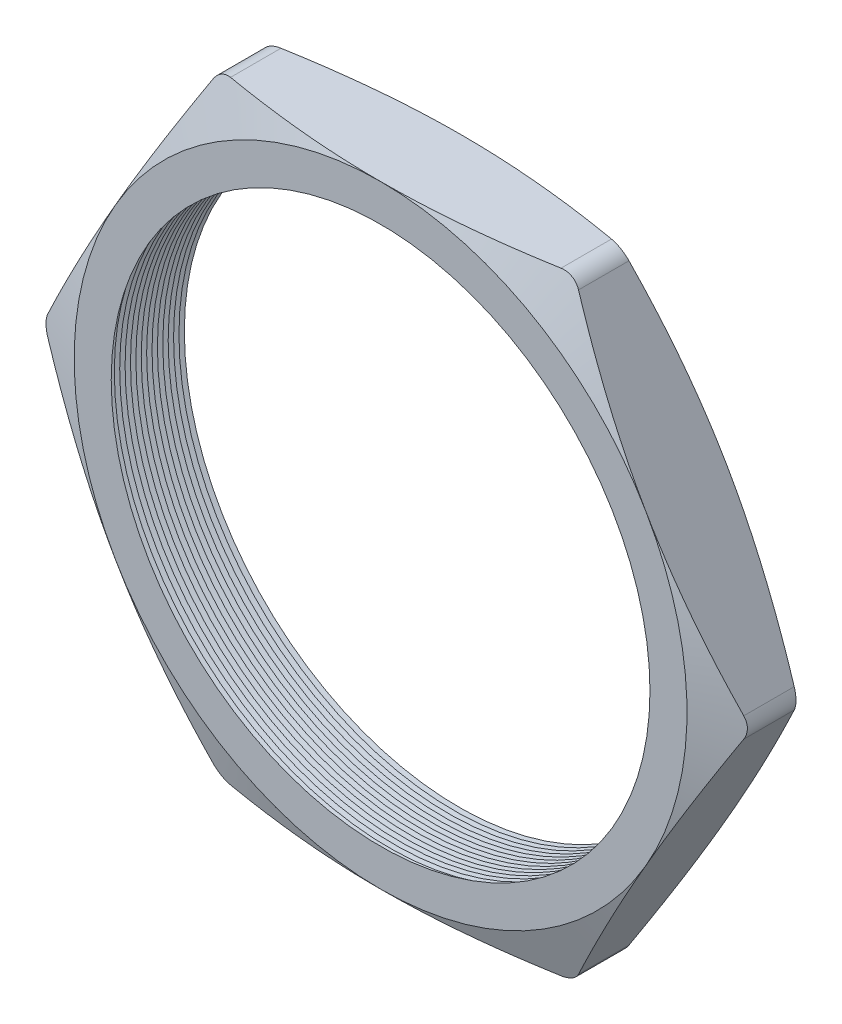
SolidWorks part; units mm, degrees
ref_plane "Front Plane" through (0, 0, 0) normal (0, 0, 1) x (1, 0, 0)
ref_plane "Top Plane" through (0, 0, 0) normal (0, 1, 0) x (1, 0, 0)
ref_plane "Right Plane" through (0, 0, 0) normal (1, 0, 0) x (0, 0, -1)
sketch "Sketch1" plane through (0, 0, 0) normal (0, 0, 1) x (1, 0, 0)
  line L1 (-13.3449, 0) -> (-6.6724, -11.557)
  line L2 (-6.6724, -11.557) -> (6.6724, -11.557)
  line L3 (6.6724, -11.557) -> (13.3449, 0)
  line L4 (13.3449, 0) -> (6.6724, 11.557)
  line L5 (6.6724, 11.557) -> (-6.6724, 11.557)
  line L6 (-6.6724, 11.557) -> (-13.3449, 0)
  circle A0 centre (0, 0) radius 11.557 construction
  circle A1 centre (0, 0) radius 10.16
  dimension "TS" = 20.32
  dimension "H" = 23.114
extrude "Extrude1" add sketch "Sketch1" along normal blind 3.048
fillet "Fillet1" radius 0.762 6 edges at (-6.6724, 11.557, 1.524) (-13.3449, 0, 1.524) (-6.6724, -11.557, 1.524) (6.6724, -11.557, 1.524) (13.3449, 0, 1.524) (6.6724, 11.557, 1.524)
sketch "Sketch2" plane through (0, 0, 3.048) normal (0, 0, 1) x (1, 0, 0)
  line L0 (6.2325, 11.557) -> (-6.2325, 11.557) construction
  circle A0 centre (0, 0) radius 11.557
extrude "Cut-Extrude1" cut sketch "Sketch2" against normal through all draft 70 flip side to cut
sketch "Sketch3" plane through (0, 0, 0) normal (0, 0, -1) x (-1, 0, 0)
  circle A0 centre (0, 0) radius 11.557
extrude "Cut-Extrude2" cut sketch "Sketch3" against normal through all draft 70 flip side to cut
sketch "Sketch4" plane through (0, 0, 0) normal (0, 1, 0) x (1, 0, 0)
  line L0 (-10.16, -3.048) -> (-10.16, -2.6081)
  line L2 (-10.16, -2.6081) -> (-10.541, -2.828)
  line L3 (-10.541, -2.828) -> (-10.16, -3.048)
  line L5 (-10.16, 0) -> (-10.16, -3.048) construction
  line L6 (-10.16, -3.048) -> (10.16, -3.048) construction
  dimension "D1" = 60
  dimension "D2" = 60
  dimension "D3" = 0.381
revolve "Cut-Revolve1" cut sketch "Sketch4" angle 360 about axis through (0, 0, 3.048) along (0, 0, -1)
pattern_linear "LPattern1" count 15 spacing 0.2032 along (0, 0, -1) of "Cut-Revolve1"
